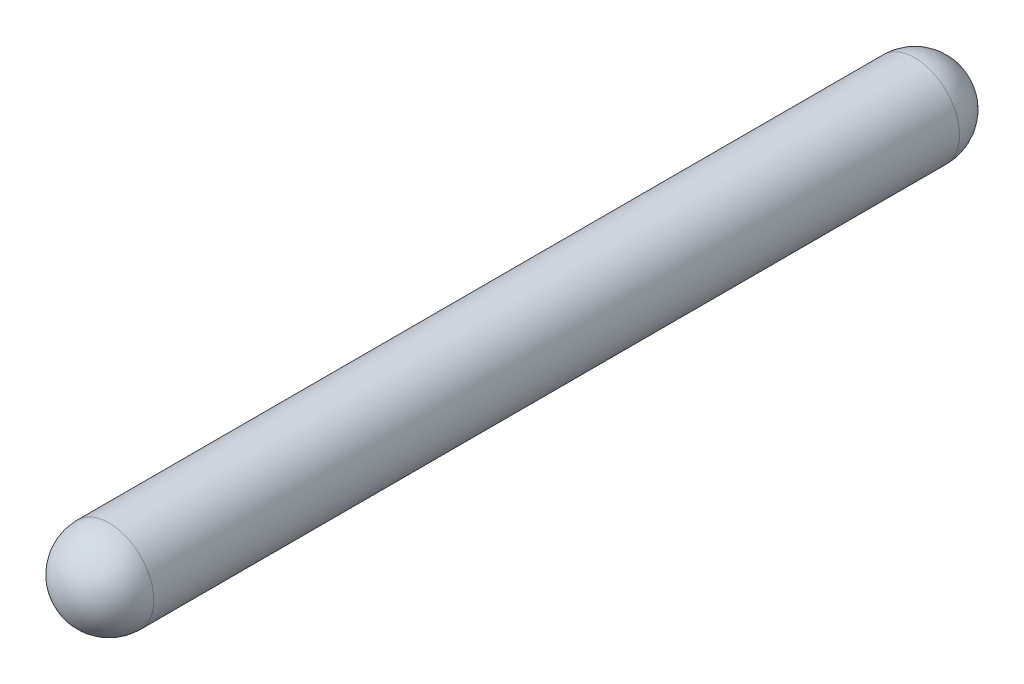
SolidWorks part; units mm, degrees
material "AISI 1020"
ref_plane "Front Plane" through (0, 0, 0) normal (0, 0, 1) x (1, 0, 0)
ref_plane "Top Plane" through (0, 0, 0) normal (0, 1, 0) x (1, 0, 0)
ref_plane "Right Plane" through (0, 0, 0) normal (1, 0, 0) x (0, 0, -1)
sketch "Sketch1" plane through (0, 0, 0) normal (0, 0, 1) x (1, 0, 0)
  circle A0 centre (0, 0) radius 1.5
  dimension "D1" = 3
extrude "Boss-Extrude1" add sketch "Sketch1" along normal blind 30
fillet "Fillet1" radius 1.5 2 edges at (1.5, 0, 0) (1.5, 0, 30)
scale "Scale1" scale about centroid uniform scaling yes scale factor 2
